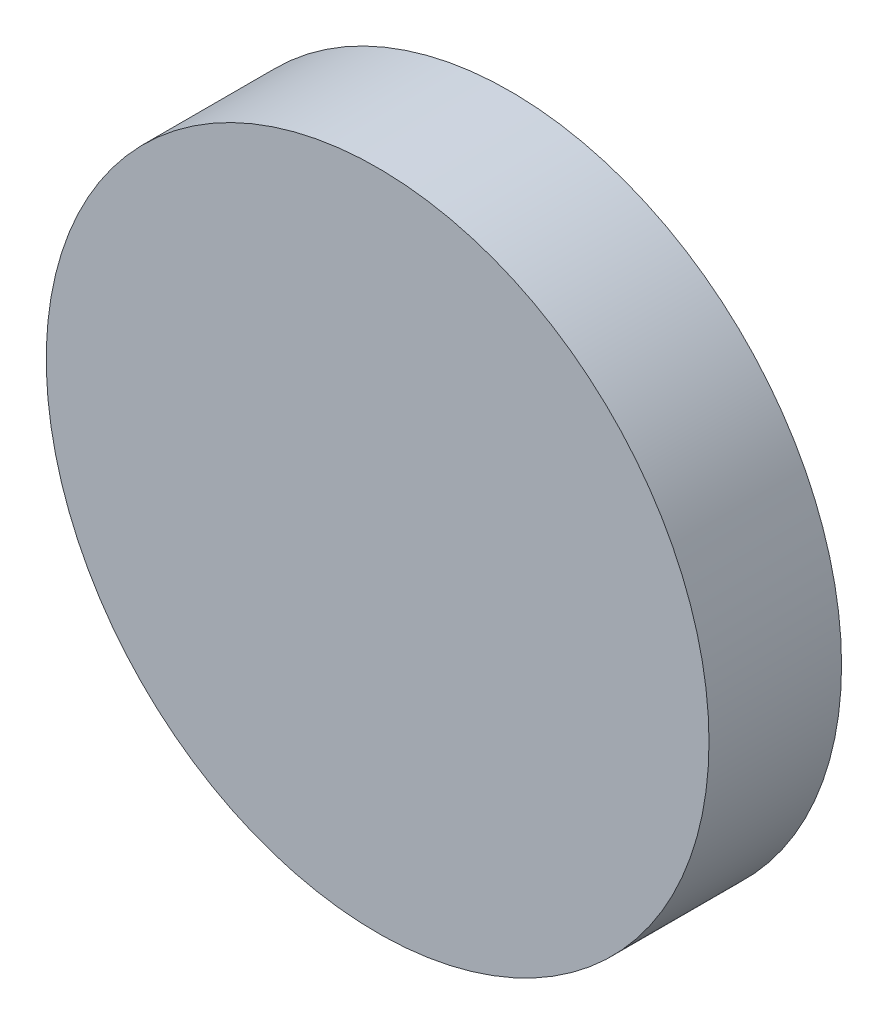
SolidWorks part; units mm, degrees
ref_plane "前视基准面" through (0, 0, 0) normal (0, 0, 1) x (1, 0, 0)
ref_plane "上视基准面" through (0, 0, 0) normal (0, 1, 0) x (1, 0, 0)
ref_plane "右视基准面" through (0, 0, 0) normal (1, 0, 0) x (0, 0, -1)
sketch "草图1" plane through (0, 0, 0) normal (0, 0, 1) x (1, 0, 0)
  circle A0 centre (0, 0) radius 25
  dimension "D1" = 50
extrude "凸台-拉伸1" add sketch "草图1" along normal blind 10 contours A0
